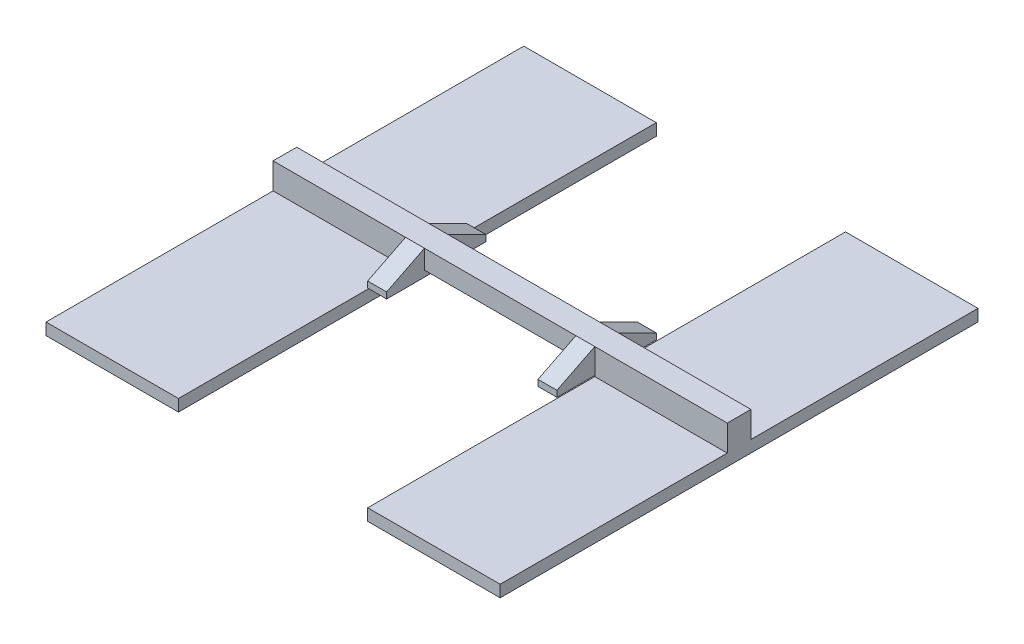
SolidWorks part; units mm, degrees
ref_plane "Front Plane" through (0, 0, 0) normal (0, 0, 1) x (1, 0, 0)
ref_plane "Top Plane" through (0, 0, 0) normal (0, 1, 0) x (1, 0, 0)
ref_plane "Right Plane" through (0, 0, 0) normal (1, 0, 0) x (0, 0, -1)
sketch "Sketch1" plane through (0, 0, 0) normal (0, 0, 1) x (1, 0, 0)
  line L10 (1, 0) -> (9, 0)
  line L12 (0, 1) -> (10, 1)
  line L14 (0, 1) -> (-7, 1)
  line L15 (0, -0.325) -> (0, -1)
  line L16 (0, -1) -> (-7, -1)
  line L17 (-7, 1) -> (-7, -1)
  line L18 (10, 1) -> (17, 1)
  line L19 (10, -0.325) -> (10, -1)
  line L20 (10, -1) -> (17, -1)
  line L21 (17, 1) -> (17, -1)
  line L24 (0, -0.325) -> (1, -0.325)
  line L25 (1, 0) -> (1, -0.325)
  line L28 (10, -0.325) -> (9, -0.325)
  line L29 (9, 0) -> (9, -0.325)
extrude "Boss-Extrude1" add sketch "Sketch1" along normal blind 1.25
sketch "Sketch2" plane through (0, 0, 1.25) normal (0, 0, 1) x (1, 0, 0)
  line L1 (1, -0.325) -> (0, -0.325)
  line L2 (1, -0.325) -> (1, 0)
  line L3 (1, 0) -> (0, 0)
  line L4 (0, -0.325) -> (0, 0)
  line L5 (9, -0.325) -> (10, -0.325)
  line L6 (9, -0.325) -> (9, 0)
  line L7 (9, 0) -> (10, 0)
  line L8 (10, -0.325) -> (10, 0)
  dimension "D1" = 0.325
  dimension "D2" = 1
extrude "Boss-Extrude2" add sketch "Sketch2" along normal blind 2
sketch "Sketch3" plane through (0, 0, 0) normal (0, 0, -1) x (-1, 0, 0)
  line L1 (-9, -0.325) -> (-10, -0.325)
  line L2 (-9, -0.325) -> (-9, 0)
  line L3 (-9, 0) -> (-10, 0)
  line L4 (-10, -0.325) -> (-10, 0)
  line L5 (-1, -0.325) -> (0, -0.325)
  line L6 (-1, -0.325) -> (-1, 0)
  line L7 (-1, 0) -> (0, 0)
  line L8 (0, -0.325) -> (0, 0)
  dimension "D1" = 1
  dimension "D2" = 0.325
  dimension "D3" = 1
  dimension "D4" = 0.325
extrude "Boss-Extrude3" add sketch "Sketch3" along normal blind 2
sketch "Sketch7" plane through (10, 0, 0) normal (1, 0, 0) x (0, 0, -1)
  line L0 (-3.25, 0) -> (-1.25, 1)
  line L1 (-1.25, 1) -> (-1.25, 0)
  line L2 (2, 0) -> (0, 1)
  line L3 (0, 1) -> (0, 0)
  line L4 (0, 0) -> (2, 0)
  line L6 (-1.25, -0.325) -> (-1.25, 0)
  line L7 (-1.25, 0) -> (-3.25, 0)
  line L8 (-3.25, 0) -> (-3.25, -0.325)
  line L9 (-3.25, -0.325) -> (-1.25, -0.325)
  line L10 (-1.25, -0.325) -> (-1.25, 0)
  line L12 (-3.25, 0) -> (-3.25, -0.325)
  line L13 (-3.25, -0.325) -> (-1.25, -0.325)
  dimension "D1" = 0
extrude "Boss-Extrude7" add sketch "Sketch7" against normal blind 1
sketch "Sketch8" plane through (0, 0, 0) normal (-1, 0, 0) x (0, 0, 1)
  line L0 (-2, 0) -> (0, 1)
  line L1 (0, 1) -> (0, 0)
  line L2 (0, 0) -> (-2, 0)
  line L3 (1.25, 1) -> (1.25, 0)
  line L4 (1.25, 0) -> (3.25, 0)
  line L5 (3.25, 0) -> (1.25, 1)
extrude "Boss-Extrude8" add sketch "Sketch8" against normal blind 1
sketch "Sketch9" plane through (0, 0, 1.25) normal (0, 0, 1) x (1, 0, 0)
  line L0 (-7, 1) -> (-7, -1) construction
  line L1 (0, -1) -> (-7, -1)
  line L2 (0, -1) -> (0, -0.3758)
  line L3 (0, -0.3758) -> (-7, -0.3758)
  line L4 (-7, -1) -> (-7, -0.3758)
  line L5 (17, -1) -> (17, 1) construction
  line L6 (10, -1) -> (17, -1)
  line L7 (10, -1) -> (10, -0.3758)
  line L8 (10, -0.3758) -> (17, -0.3758)
  line L9 (17, -1) -> (17, -0.3758)
extrude "Boss-Extrude9" add sketch "Sketch9" along normal blind 12 and the other way blind 13.25
